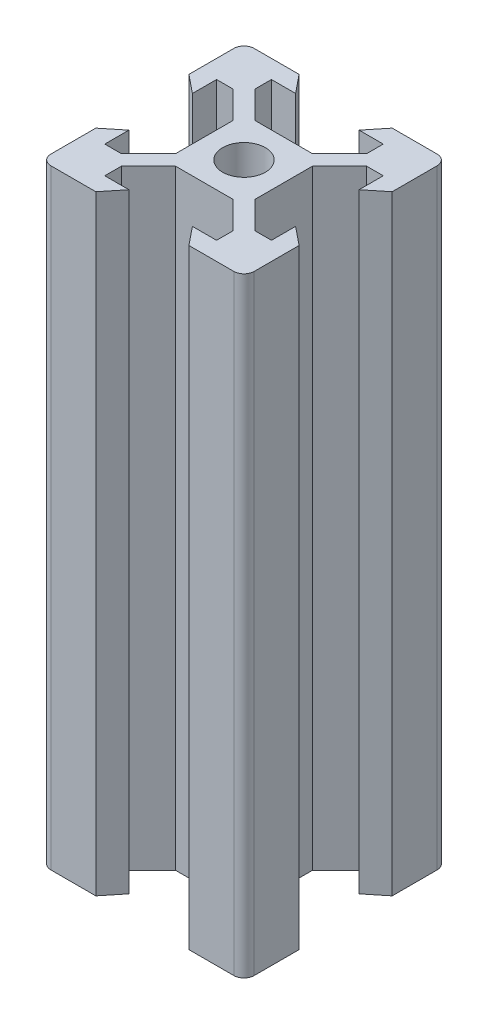
SolidWorks part; units mm, degrees
ref_plane "Front Plane" through (0, 0, 0) normal (0, 0, 1) x (1, 0, 0)
ref_plane "Top Plane" through (0, 0, 0) normal (0, 1, 0) x (1, 0, 0)
ref_plane "Right Plane" through (0, 0, 0) normal (1, 0, 0) x (0, 0, -1)
sketch "Sketch1" plane through (0, 0, 0) normal (0, 1, 0) x (1, 0, 0)
  line L0 (-3.125, 8.2) -> (-4.58, 10)
  line L1 (-9, 10) -> (9, 10)
  line L2 (-10, 9) -> (-10, -9)
  line L3 (-9, -10) -> (9, -10)
  line L4 (10, 9) -> (10, -9)
  line L5 (-10, 10) -> (10, -10) construction
  line L6 (-10, -10) -> (10, 10) construction
  line L7 (-10, 0) -> (0, 0) construction
  line L8 (0, 10) -> (0, 0) construction
  line L9 (-8.2, 3.125) -> (-10, 4.58)
  line L10 (-8.2, 3.125) -> (-8.2, 5.5)
  line L11 (-3.125, 8.2) -> (-5.5, 8.2)
  line L12 (-5.5, 8.2) -> (-5.5, 6.56)
  line L13 (-2.84, 3.9) -> (2.84, 3.9)
  line L14 (-5.5, 6.56) -> (-2.84, 3.9)
  line L15 (-8.2, 5.5) -> (-6.56, 5.5)
  line L16 (-6.56, 5.5) -> (-3.9, 2.84)
  line L17 (-3.9, 2.84) -> (-3.9, -2.84)
  line L18 (3.9, 2.84) -> (3.9, -2.84)
  line L19 (6.56, 5.5) -> (3.9, 2.84)
  line L20 (8.2, 5.5) -> (6.56, 5.5)
  line L21 (8.2, 3.125) -> (8.2, 5.5)
  line L22 (8.2, 3.125) -> (10, 4.58)
  line L23 (3.125, 8.2) -> (4.58, 10)
  line L24 (3.125, 8.2) -> (5.5, 8.2)
  line L25 (5.5, 8.2) -> (5.5, 6.56)
  line L26 (5.5, 6.56) -> (2.84, 3.9)
  line L27 (-8.2, -3.125) -> (-10, -4.58)
  line L28 (-8.2, -3.125) -> (-8.2, -5.5)
  line L29 (-8.2, -5.5) -> (-6.56, -5.5)
  line L30 (-6.56, -5.5) -> (-3.9, -2.84)
  line L31 (8.2, -3.125) -> (10, -4.58)
  line L32 (8.2, -3.125) -> (8.2, -5.5)
  line L33 (8.2, -5.5) -> (6.56, -5.5)
  line L34 (6.56, -5.5) -> (3.9, -2.84)
  line L35 (5.5, -6.56) -> (2.84, -3.9)
  line L36 (5.5, -8.2) -> (5.5, -6.56)
  line L37 (3.125, -8.2) -> (5.5, -8.2)
  line L38 (3.125, -8.2) -> (4.58, -10)
  line L39 (-5.5, -6.56) -> (-2.84, -3.9)
  line L40 (-2.84, -3.9) -> (2.84, -3.9)
  line L41 (-5.5, -8.2) -> (-5.5, -6.56)
  line L42 (-3.125, -8.2) -> (-5.5, -8.2)
  line L43 (-3.125, -8.2) -> (-4.58, -10)
  circle A0 centre (0, 0) radius 2.1
  arc A1 (-10, -9) -> (-9, -10) centre (-9, -9) ccw
  arc A2 (9, -10) -> (10, -9) centre (9, -9) ccw
  arc A3 (9, 10) -> (10, 9) centre (9, 9) cw
  arc A4 (-9, 10) -> (-10, 9) centre (-9, 9) ccw
  point P0 (0, 0)
  point P35 (0, 3.9)
  point P40 (-3.9, 0)
  point P41 (3.9, 0)
  dimension "D3" = 4.2
  dimension "D2" = 1
  dimension "D1" = 20
  dimension "D4" = 6.1
  dimension "D5" = 6.25
  dimension "D6" = 11
  dimension "D7" = 5.68
  dimension "D8" = 9.16
  dimension "D9" = 1.8
extrude "Boss-Extrude1" add sketch "Sketch1" along normal blind 60 contours L43 L42 L41 L39 L40 L35 L36 L37 L38 L3 L4 L31 L32 L33 L34 L18 L19 L20 L21 L22 L1 L23 L24 L25 L26 L13 L14 L12 L11 L0 L2 L9 L10 L15 L16 L17 L30 L29 L28 L27 A0
